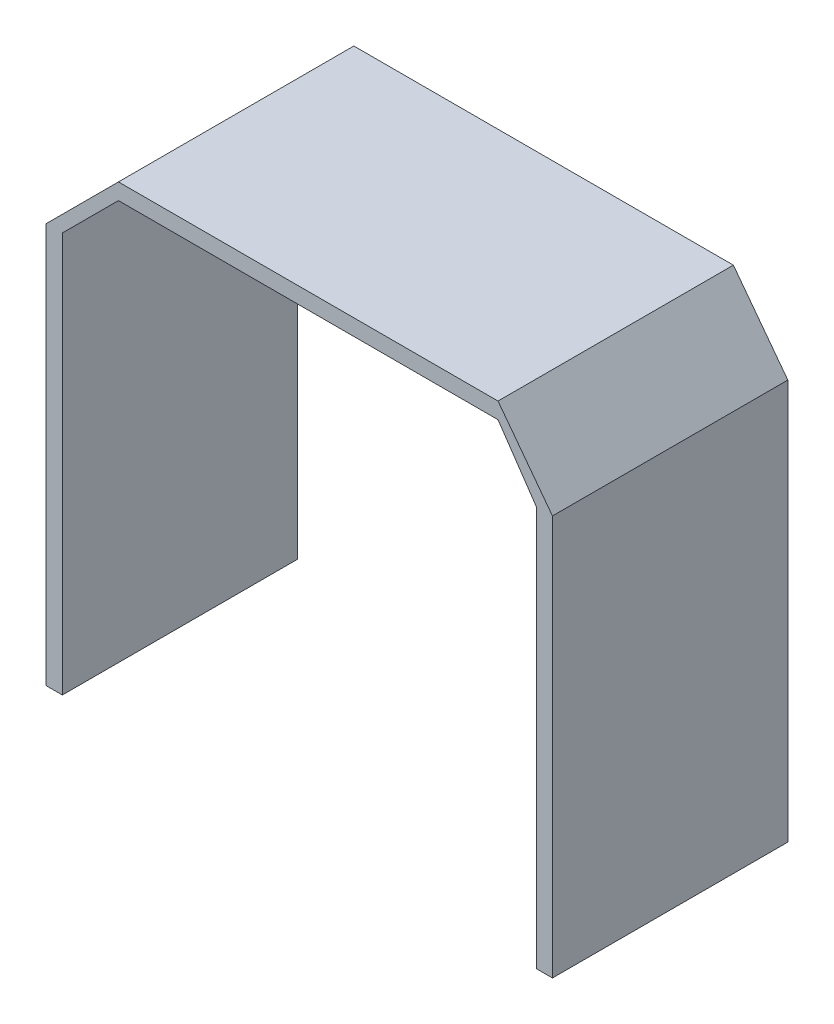
SolidWorks part; units mm, degrees
ref_plane "Front Plane" through (0, 0, 0) normal (0, 0, 1) x (1, 0, 0)
ref_plane "Top Plane" through (0, 0, 0) normal (0, 1, 0) x (1, 0, 0)
ref_plane "Right Plane" through (0, 0, 0) normal (1, 0, 0) x (0, 0, -1)
sketch "Sketch1" plane through (0, 0, 0) normal (0, 0, 1) x (1, 0, 0)
  line L0 (0, 0) -> (0, 54.4)
  line L2 (-5.2012, 64.2289) -> (-56.8012, 64.2289)
  line L3 (-56.8012, 64.2289) -> (-66.6301, 54.4)
  line L4 (-66.6301, 54.4) -> (-66.6301, 0)
  line L5 (-66.6301, 0) -> (-64.4301, 0)
  line L6 (-64.4301, 0) -> (-64.4301, 54.4)
  line L7 (-64.4301, 54.4) -> (-56.8012, 62.0289)
  line L8 (-56.8012, 62.0289) -> (-5.2012, 62.0289)
  line L10 (2.2, 54.4) -> (2.2, 0.0003)
  line L11 (0, 0) -> (2.2, 0.0003)
  line L12 (-5.2012, 62.0289) -> (0, 54.4)
  line L13 (-5.2012, 64.2289) -> (2.2, 54.4)
  dimension "D1" = 2.2
  dimension "D2" = 2.2
  dimension "D3" = 2.2
extrude "Boss-Extrude1" add sketch "Sketch1" along normal blind 32 contours L4 L5 L6 L7 L8 L12 L0 L11 L10 L13 L2 L3
